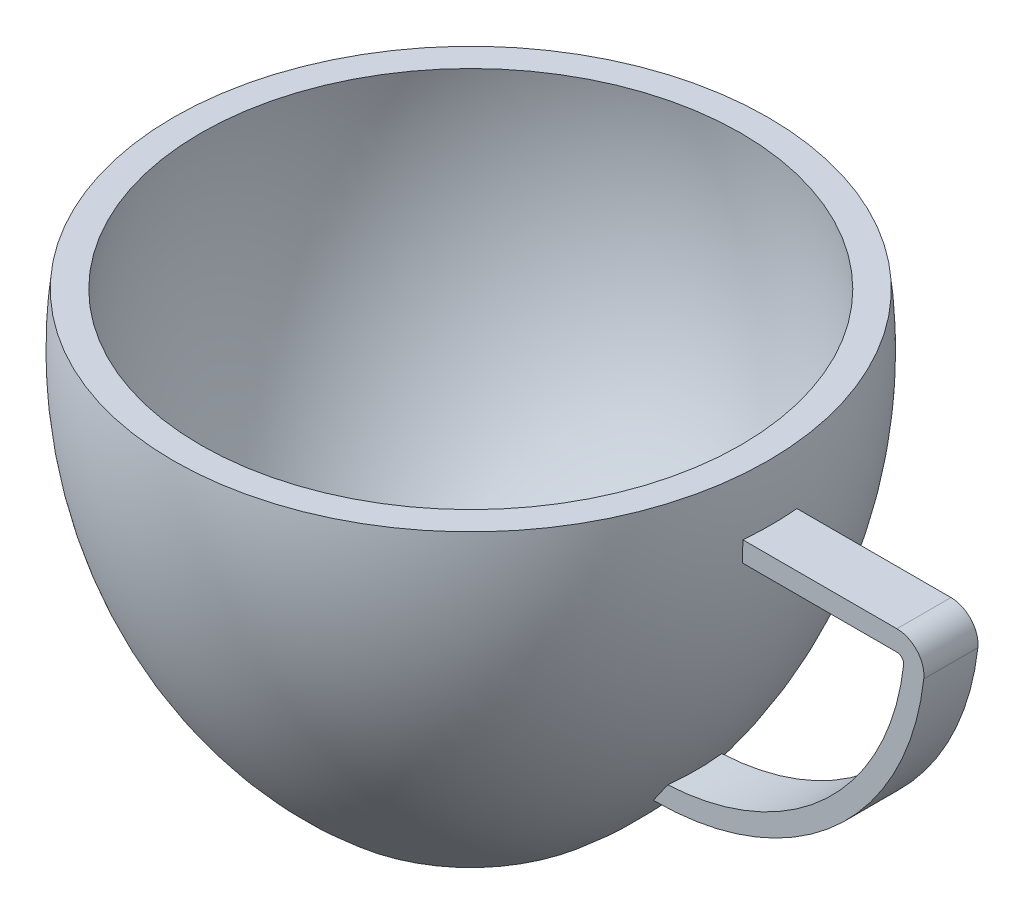
SolidWorks part; units mm, degrees
material "Commercially Pure CP-Ti UNS R50400 (SS)"
ref_plane "Front Plane" through (0, 0, 0) normal (0, 0, 1) x (1, 0, 0)
ref_plane "Top Plane" through (0, 0, 0) normal (0, 1, 0) x (1, 0, 0)
ref_plane "Right Plane" through (0, 0, 0) normal (1, 0, 0) x (0, 0, -1)
sketch "Sketch1" plane through (0, 0, 0) normal (0, 0, 1) x (1, 0, 0)
  line L0 (0, 0) -> (0, 15)
  line L1 (0, 0) -> (-5, 0)
  line L2 (-11, 15) -> (0, 15)
  arc A0 (-5, 0) -> (-11, 15) centre (5.8884, 13.0554) cw
  dimension "D3" = 17
  dimension "D1" = 5
  dimension "D2" = 15
  dimension "D4" = 11
revolve "Revolve1" add sketch "Sketch1" angle 360 about L0
sketch "Sketch2" plane through (0, 0, 0) normal (0, 0, 1) x (1, 0, 0)
  line L0 (0, 0) -> (0, 15)
  line L1 (11, 15) -> (-11, 15) construction
  line L2 (-9.9904, 15.021) -> (0, 15)
  line L5 (-4.6315, 1) -> (5, 1)
  line L6 (-4.6315, 1) -> (0, 1)
  arc A3 (-10.0066, 14.8856) -> (-4.6315, 1) centre (5.8884, 13.0554) ccw
  arc A4 (-9.9904, 15.021) -> (-4.6315, 1) centre (5.8884, 13.0554) ccw
  dimension "D2" = 9.9904
  dimension "D1" = 1
revolve "Cut-Revolve1" cut sketch "Sketch2" angle 360 about L0
sketch "Sketch4" plane through (0, 0, 0) normal (0, 0, 1) x (1, 0, 0)
  line L0 (10.5, 13) -> (16.7631, 13)
  line L1 (7.8189, 3) -> (7.3143, 3)
  line L2 (-5, 0) -> (5, 0) construction
  line L5 (11, 15) -> (-11, 15) construction
  arc A0 (17.757, 11.8889) -> (7.8189, 3) centre (7.8189, 13) cw
  arc A1 (5, 0) -> (11, 15) centre (-5.8884, 13.0554) ccw construction
  arc A2 (16.7631, 13) -> (17.757, 11.8889) centre (16.7631, 12) cw
  point P10 (0, 0)
  point P11 (0, 0)
  point P12 (0, 0)
  point P13 (0, 0)
  point P14 (0, 0)
  dimension "D2" = 2
  dimension "D3" = 10
  dimension "D6" = 1
  dimension "D1" = 3
  dimension "D4" = 0.5
  dimension "D5" = 0.5046
extrude "Extrude-Thin1" add sketch "Sketch4" along normal mid plane 2 thin
